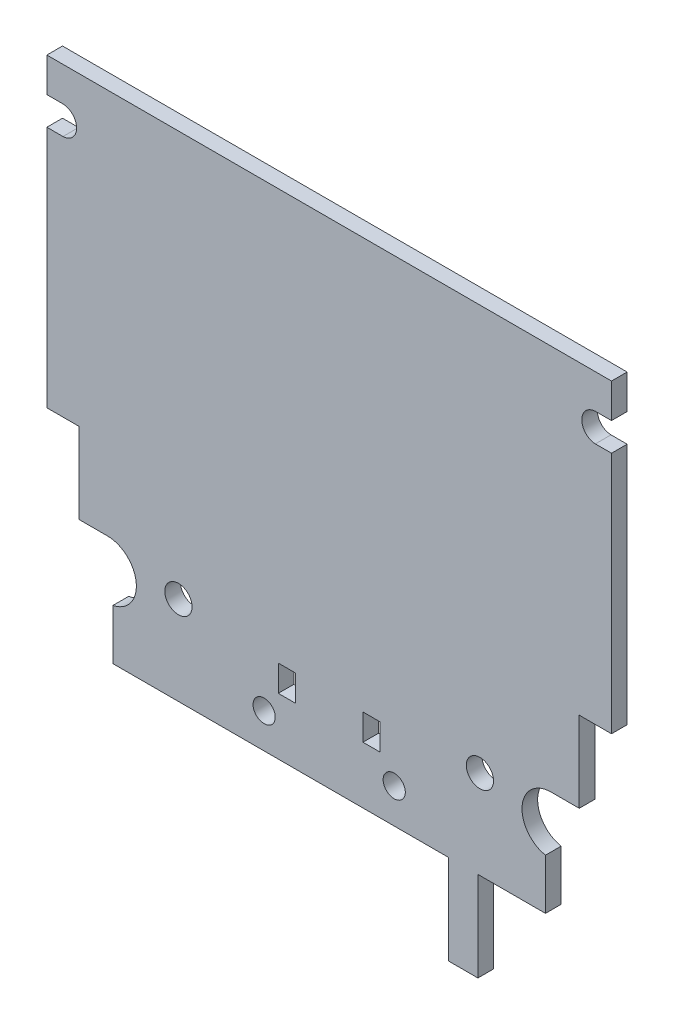
SolidWorks part; units mm, degrees
ref_plane "Ebene vorne" through (0, 0, 0) normal (0, 0, 1) x (1, 0, 0)
ref_plane "Ebene oben" through (0, 0, 0) normal (0, 1, 0) x (1, 0, 0)
ref_plane "Ebene rechts" through (0, 0, 0) normal (1, 0, 0) x (0, 0, -1)
sketch "Skizze1" plane through (0, 0, 0) normal (0, 0, 1) x (1, 0, 0)
  line L0 (-28, 23.3034) -> (-28, 26.7034)
  line L1 (-5.05, -14.0457) -> (-5.05, -16.6457)
  line L2 (-21.45, -22.2966) -> (11.85, -22.2966)
  line L3 (-28, -3.5966) -> (-28, 20.5034)
  line L4 (-28, 26.7034) -> (28, 26.7034)
  line L5 (28, -3.5966) -> (28, 20.5034)
  line L6 (-1000, 0) -> (49000, 0) construction
  line L7 (0, -1000) -> (0, 49000) construction
  line L8 (14.75, -22.2966) -> (14.75, -31.1966)
  line L9 (14.75, -31.1966) -> (11.85, -31.1966)
  line L10 (11.85, -22.2966) -> (11.85, -31.1966)
  line L11 (28, 23.3034) -> (26.4, 23.3034)
  line L12 (24.8, -11.5966) -> (24.8, -3.5966)
  line L13 (28, 20.5034) -> (26.4, 20.5034)
  line L14 (28, 23.3034) -> (28, 26.7034)
  line L15 (-28, 23.3034) -> (-26.4, 23.3034)
  line L16 (-24.8, -11.5966) -> (-22, -11.5966)
  line L17 (-28, 20.5034) -> (-26.4, 20.5034)
  line L18 (-21.45, -22.2966) -> (-21.45, -17.2966)
  line L19 (28, -3.5966) -> (24.8, -3.5966)
  line L20 (-24.8, -11.5966) -> (24.8, -11.5966) construction
  line L21 (24.8, -11.5966) -> (22, -11.5966)
  line L22 (21.45, -22.2966) -> (21.45, -17.2966)
  line L23 (-28, -3.5966) -> (-24.8, -3.5966)
  line L24 (-24.8, -11.5966) -> (-24.8, -3.5966)
  line L25 (14.75, -22.2966) -> (21.45, -22.2966)
  line L27 (3.35, -14.0457) -> (5.05, -14.0457)
  line L28 (3.35, -14.0457) -> (3.35, -16.6457)
  line L29 (3.35, -16.6457) -> (5.05, -16.6457)
  line L30 (5.05, -14.0457) -> (5.05, -16.6457)
  line L31 (-3.35, -16.6457) -> (-5.05, -16.6457)
  line L32 (-3.35, -14.0457) -> (-3.35, -16.6457)
  line L33 (-3.35, -14.0457) -> (-5.05, -14.0457)
  arc A0 (-26.4, 23.3034) -> (-26.4, 20.5034) centre (-26.4509, 21.9034) cw
  arc A1 (26.4, 23.3034) -> (26.4, 20.5034) centre (26.4509, 21.9034) ccw
  arc A2 (21.45, -17.2966) -> (22, -11.5966) centre (22, -14.4731) cw
  arc A3 (-21.45, -17.2966) -> (-22, -11.5966) centre (-22, -14.4731) ccw
  circle A4 centre (14.95, -13.4966) radius 1.35
  circle A5 centre (-14.95, -13.4966) radius 1.35
  circle A6 centre (6.45, -18.852) radius 1.1
  circle A7 centre (-6.45, -18.852) radius 1.1
  point P2 (0, 0)
  point P25 (21.45, -17.2966)
  dimension "D15" = 8.8
  dimension "D17" = 15
  dimension "D18" = 2.2
  dimension "D19" = 1.7
  dimension "D1" = 56
  dimension "D2" = 49
  dimension "D3" = 8.9
  dimension "D4" = 2.9
  dimension "D5" = 3.4
  dimension "D6" = 30.3
  dimension "D7" = 3.2
  dimension "D8" = 3.4
  dimension "D9" = 3.2
  dimension "D10" = 30.3
  dimension "D11" = 2.8
  dimension "D12" = 6.7
  dimension "D13" = 8
  dimension "D14" = 5
  dimension "D16" = 9.85
  dimension "D20" = 2.6
  dimension "D21" = 16.4
  dimension "D22" = 42.9
  dimension "D23" = 1.6
  dimension "D24" = 1.6
extrude "Aufsatz-Linear austragen1" add sketch "Skizze1" along normal blind 1.55
